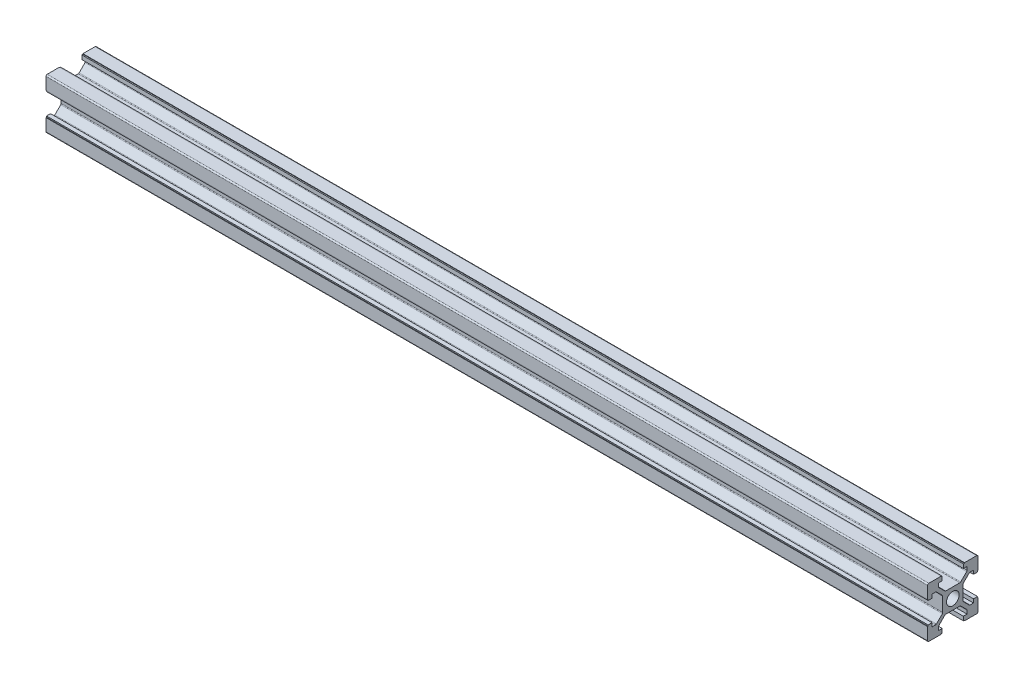
SolidWorks part; units mm, degrees
ref_plane "Ön Düzlem" through (0, 0, 0) normal (0, 0, 1) x (1, 0, 0)
ref_plane "Üst Düzlem" through (0, 0, 0) normal (0, 1, 0) x (1, 0, 0)
ref_plane "Sağ Düzlem" through (0, 0, 0) normal (1, 0, 0) x (0, 0, -1)
sketch "Çizim1" plane through (0, 0, 0) normal (1, 0, 0) x (0, 0, -1)
  line L0 (-9.5, 10) -> (-4.65, 10)
  line L1 (9.5, -10) -> (4.65, -10)
  line L2 (-2.7929, 4) -> (2.7929, 4)
  line L3 (4, 2.7929) -> (4, -2.7929)
  line L4 (2.7929, -4) -> (-2.7929, -4)
  line L5 (-4, -2.7929) -> (-4, 2.7929)
  line L6 (-4.65, 10) -> (-4.65, 9.8)
  line L7 (4.65, 10) -> (4.65, 9.8)
  line L8 (-4.2, 9.8) -> (-4.2, 8.2)
  line L9 (4.2, 9.8) -> (4.2, 8.2)
  line L10 (4.65, 10) -> (9.5, 10)
  line L11 (4.2, 9.8) -> (4.65, 9.8)
  line L12 (-4.65, 9.8) -> (-4.2, 9.8)
  line L13 (4.2, 8.2) -> (5.65, 8.2)
  line L14 (-5.65, 8.2) -> (-5.65, 6.8571)
  line L15 (-5.5036, 6.5036) -> (-3.1464, 4.1464)
  line L16 (5.65, 8.2) -> (5.65, 6.8571)
  line L17 (5.5036, 6.5036) -> (3.1464, 4.1464)
  line L18 (-5.65, 8.2) -> (-4.2, 8.2)
  line L19 (-5.65, -8.2) -> (-4.2, -8.2)
  line L20 (4.2, -8.2) -> (5.65, -8.2)
  line L21 (-4.65, -10) -> (-4.65, -9.8)
  line L22 (4.65, -10) -> (4.65, -9.8)
  line L23 (-4.2, -9.8) -> (-4.2, -8.2)
  line L24 (4.2, -9.8) -> (4.2, -8.2)
  line L25 (-4.65, -9.8) -> (-4.2, -9.8)
  line L26 (4.2, -9.8) -> (4.65, -9.8)
  line L27 (-5.65, -8.2) -> (-5.65, -6.8571)
  line L28 (-5.5036, -6.5036) -> (-3.1464, -4.1464)
  line L29 (5.65, -8.2) -> (5.65, -6.8571)
  line L30 (5.5036, -6.5036) -> (3.1464, -4.1464)
  line L31 (-4.65, -10) -> (-9.5, -10)
  line L32 (-10, -9.5) -> (-10, -4.65)
  line L33 (-10, 4.65) -> (-10, 9.5)
  line L34 (10, 9.5) -> (10, 4.65)
  line L35 (10, -4.65) -> (10, -9.5)
  line L36 (-8.2, -5.65) -> (-8.2, -4.2)
  line L37 (-8.2, 4.2) -> (-8.2, 5.65)
  line L38 (-10, -4.65) -> (-9.8, -4.65)
  line L39 (-10, 4.65) -> (-9.8, 4.65)
  line L40 (-9.8, -4.2) -> (-8.2, -4.2)
  line L41 (-9.8, 4.2) -> (-8.2, 4.2)
  line L42 (-9.8, -4.65) -> (-9.8, -4.2)
  line L43 (-9.8, 4.2) -> (-9.8, 4.65)
  line L44 (-8.2, -5.65) -> (-6.8571, -5.65)
  line L45 (-6.5036, -5.5036) -> (-4.1464, -3.1464)
  line L46 (-8.2, 5.65) -> (-6.8571, 5.65)
  line L47 (-6.5036, 5.5036) -> (-4.1464, 3.1464)
  line L48 (8.2, -5.65) -> (8.2, -4.2)
  line L49 (8.2, 4.2) -> (8.2, 5.65)
  line L50 (10, -4.65) -> (9.8, -4.65)
  line L51 (10, 4.65) -> (9.8, 4.65)
  line L52 (9.8, -4.2) -> (8.2, -4.2)
  line L53 (9.8, 4.2) -> (8.2, 4.2)
  line L54 (9.8, -4.65) -> (9.8, -4.2)
  line L55 (9.8, 4.2) -> (9.8, 4.65)
  line L56 (8.2, -5.65) -> (6.8571, -5.65)
  line L57 (6.5036, -5.5036) -> (4.1464, -3.1464)
  line L58 (8.2, 5.65) -> (6.8571, 5.65)
  line L59 (6.5036, 5.5036) -> (4.1464, 3.1464)
  circle A0 centre (0, 0) radius 2.5
  arc A1 (-6.8571, 5.65) -> (-6.5036, 5.5036) centre (-6.8571, 5.15) cw
  arc A2 (-5.65, 6.8571) -> (-5.5036, 6.5036) centre (-5.15, 6.8571) ccw
  arc A3 (5.65, 6.8571) -> (5.5036, 6.5036) centre (5.15, 6.8571) cw
  arc A4 (6.8571, 5.65) -> (6.5036, 5.5036) centre (6.8571, 5.15) ccw
  arc A5 (5.65, -6.8571) -> (5.5036, -6.5036) centre (5.15, -6.8571) ccw
  arc A6 (6.8571, -5.65) -> (6.5036, -5.5036) centre (6.8571, -5.15) cw
  arc A7 (4, 2.7929) -> (4.1464, 3.1464) centre (4.5, 2.7929) cw
  arc A8 (2.7929, 4) -> (3.1464, 4.1464) centre (2.7929, 4.5) ccw
  arc A9 (-2.7929, 4) -> (-3.1464, 4.1464) centre (-2.7929, 4.5) cw
  arc A10 (-4, 2.7929) -> (-4.1464, 3.1464) centre (-4.5, 2.7929) ccw
  arc A11 (-5.65, -6.8571) -> (-5.5036, -6.5036) centre (-5.15, -6.8571) cw
  arc A12 (-6.8571, -5.65) -> (-6.5036, -5.5036) centre (-6.8571, -5.15) ccw
  arc A13 (4, -2.7929) -> (4.1464, -3.1464) centre (4.5, -2.7929) ccw
  arc A14 (2.7929, -4) -> (3.1464, -4.1464) centre (2.7929, -4.5) cw
  arc A15 (-4, -2.7929) -> (-4.1464, -3.1464) centre (-4.5, -2.7929) cw
  arc A16 (-2.7929, -4) -> (-3.1464, -4.1464) centre (-2.7929, -4.5) ccw
  arc A17 (-9.5, -10) -> (-10, -9.5) centre (-9.5, -9.5) cw
  arc A18 (9.5, -10) -> (10, -9.5) centre (9.5, -9.5) ccw
  arc A19 (9.5, 10) -> (10, 9.5) centre (9.5, 9.5) cw
  arc A20 (-9.5, 10) -> (-10, 9.5) centre (-9.5, 9.5) ccw
  dimension "D1" = 0.5
extrude "Boss-Extrude1" add sketch "Çizim1" along normal blind 350
